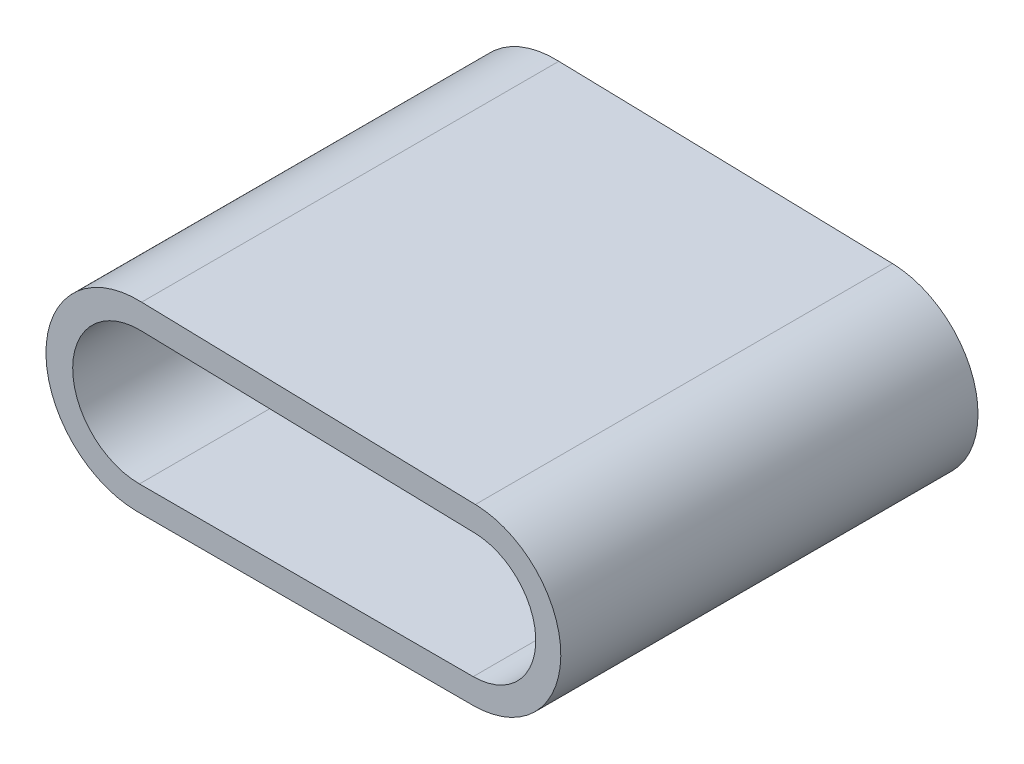
SolidWorks part; units mm, degrees
ref_plane "Front Plane" through (0, 0, 0) normal (0, 0, 1) x (1, 0, 0)
ref_plane "Top Plane" through (0, 0, 0) normal (0, 1, 0) x (1, 0, 0)
ref_plane "Right Plane" through (0, 0, 0) normal (1, 0, 0) x (0, 0, -1)
sketch "Sketch1" plane through (0, 0, 0) normal (0, 1, 0) x (1, 0, 0)
  line L1 (-15.875, -15.875) -> (15.875, -15.875)
  line L2 (-15.875, -15.875) -> (-15.875, 15.875)
  line L3 (-15.875, 15.875) -> (15.875, 15.875)
  line L4 (15.875, -15.875) -> (15.875, 15.875)
  line L5 (-15.875, -15.875) -> (15.875, 15.875) construction
  line L6 (-15.875, 15.875) -> (15.875, -15.875) construction
  point P0 (0, 0)
  dimension "D1" = 31.75
  dimension "D2" = 31.75
extrude "Boss-Extrude1" add sketch "Sketch1" along normal blind 2.54
sketch "Sketch2" plane through (0, 0, 15.875) normal (0, 0, 1) x (1, 0, 0)
  line L0 (-15.875, 0) -> (15.875, 0) construction
  line L1 (0, 0) -> (0, 2.54) construction
  line L2 (-15.875, 2.54) -> (15.875, 2.54) construction
  line L4 (10.6387, 1.905) -> (-14.7613, 1.905)
  line L6 (-14.7613, 0) -> (10.6387, 0)
  line L7 (-14.5947, 13.968) -> (10.8053, 13.3329)
  line L8 (-14.6423, 12.0636) -> (10.7577, 11.4285)
  line L11 (-14.6423, 12.0636) -> (10.7577, 11.4285) construction
  arc A0 (10.6387, 0) -> (10.8053, 13.3329) centre (10.6387, 6.6675) ccw
  arc A1 (10.6387, 1.905) -> (10.7577, 11.4285) centre (10.6387, 6.6675) ccw
  arc A6 (-14.5947, 13.968) -> (-14.7613, 0) centre (-14.8862, 6.9865) ccw
  arc A7 (-14.6423, 12.0636) -> (-14.7613, 1.905) centre (-14.7613, 6.985) ccw
  point P23 (-21.8733, 7.0699)
  point P28 (-11.5199, 14.7718)
  point P32 (-13.0525, 11.43)
  line M2 (-15.875, 0) -> (15.875, 0)
  line M4 (15.875, 2.54) -> (-15.875, 2.54)
  line M5 (-15.875, 2.54) -> (-15.875, 0)
  dimension "D1" = 9.525
  dimension "D2" = 1.905
  dimension "D3" = 25.4
  dimension "D4" = 5.08
  dimension "D5" = 7.112
  dimension "D6" = 25.4
  dimension "D7" = 25.4
  dimension "D8" = 25.4
extrude "Boss-Extrude2" add sketch "Sketch2" against normal through all contours A7 L8 A1 A0 L7 A6 M4 M5 | A7 A6 A0 A1 L4 M4 M5 M2
sketch "Sketch3" plane through (0, 0, 15.875) normal (0, 0, 1) x (1, 0, 0)
  line L0 (-15.875, 2.54) -> (-15.875, 2.0286) construction
  line L1 (-15.875, 2.54) -> (13.0146, 2.54) construction
  line L5 (15.875, 2.54) -> (15.875, 0) construction
  line L6 (-15.875, 0) -> (15.875, 0) construction
  line L8 (-15.875, 2.54) -> (-15.875, 2.0286)
  line L9 (-15.875, 2.54) -> (13.0146, 2.54)
  line L10 (15.875, 2.54) -> (15.875, 0)
  line L11 (-15.0111, 0) -> (15.875, 0)
  line L12 (-14.7613, 1.905) -> (10.6387, 1.905)
  arc A0 (-14.6423, 12.0636) -> (-15.875, 2.0286) centre (-14.7613, 6.985) ccw construction
  arc A3 (13.0146, 2.54) -> (10.7577, 11.4285) centre (10.6387, 6.6675) ccw construction
  arc A5 (-14.5947, 13.968) -> (-15.875, 0.0692) centre (-14.8862, 6.9865) ccw construction
  arc A6 (15.875, 2.54) -> (10.8053, 13.3329) centre (10.6387, 6.6675) ccw construction
  arc A7 (-14.6423, 12.0636) -> (-14.7613, 1.905) centre (-14.7613, 6.985) ccw
  arc A10 (10.6387, 1.905) -> (10.7577, 11.4285) centre (10.6387, 6.6675) ccw
  arc A11 (-14.5947, 13.968) -> (-15.0111, 0) centre (-14.8862, 6.9865) ccw
  arc A12 (10.6387, 0) -> (10.8053, 13.3329) centre (10.6387, 6.6675) ccw
extrude "Cut-Extrude1" cut sketch "Sketch3" against normal through all
ref_plane "Plane1" through (0, 0, 0) normal (0, 0, -1) x (-1, 0, 0)
ref_plane "Plane2" through (0.085, 6.7994, 0) normal (-0.0125, -0.9999, 0) x (-0.9999, 0.0125, 0)
sketch "Sketch4" plane through (0, 0, -15.875) normal (0, 0, -1) x (-1, 0, 0)
  arc A0 (-10.7577, 11.4285) -> (-10.6387, 1.905) centre (-10.6387, 6.6675) ccw construction
  point P0 (-15.4008, 6.608)
sketch "Sketch5" plane through (0, 0, 15.875) normal (0, 0, 1) x (1, 0, 0)
  point P0 (15.4008, 6.608)
